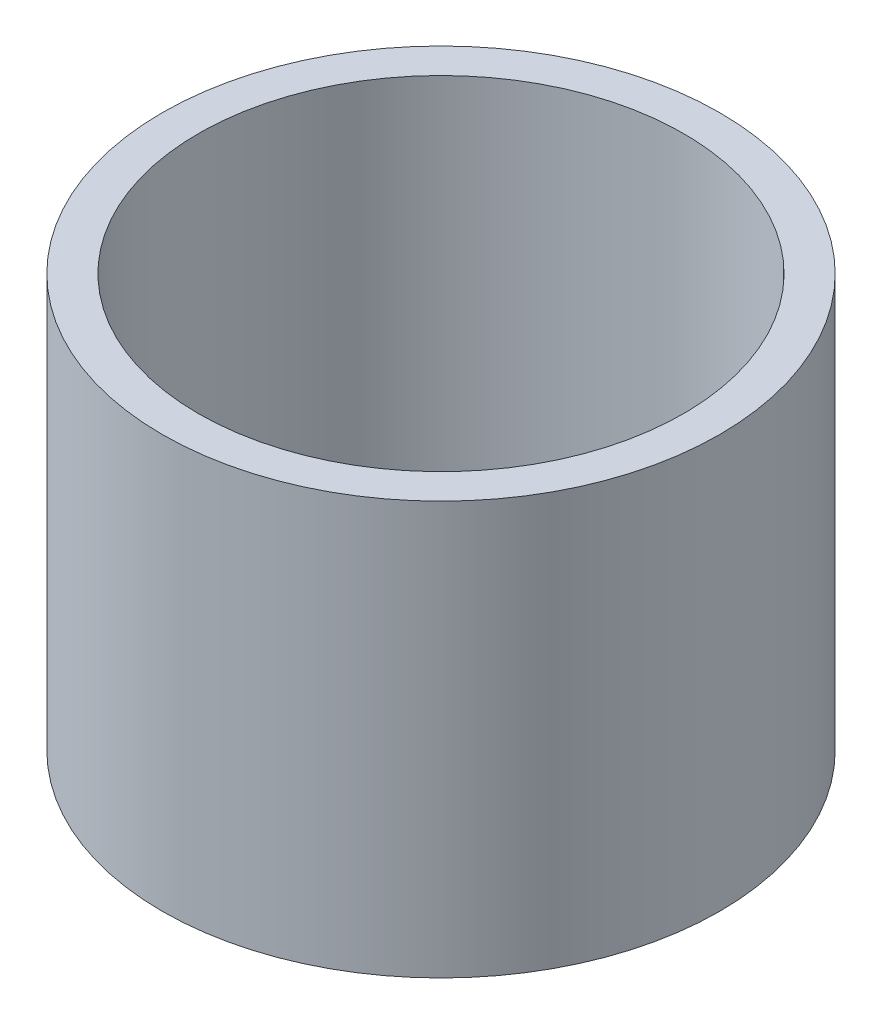
SolidWorks part; units mm, degrees
ref_plane "Front Plane" through (0, 0, 0) normal (0, 0, 1) x (1, 0, 0)
ref_plane "Top Plane" through (0, 0, 0) normal (0, 1, 0) x (1, 0, 0)
ref_plane "Right Plane" through (0, 0, 0) normal (1, 0, 0) x (0, 0, -1)
sketch "Sketch1" plane through (0, 0, 0) normal (0, 1, 0) x (1, 0, 0)
  circle A0 centre (0, 0) radius 27
  circle A1 centre (0, 0) radius 23.5
  dimension "D1" = 54
  dimension "D2" = 47
extrude "Boss-Extrude1" add sketch "Sketch1" along normal blind 40
